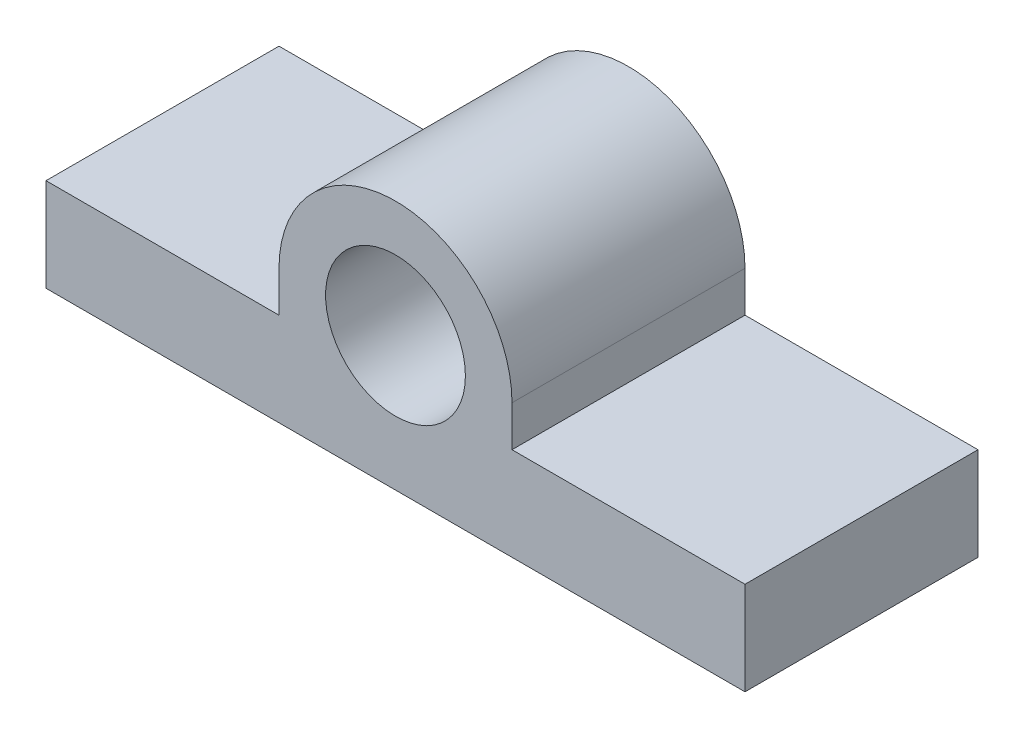
SolidWorks part; units mm, degrees
ref_plane "Front Plane" through (0, 0, 0) normal (0, 0, 1) x (1, 0, 0)
ref_plane "Top Plane" through (0, 0, 0) normal (0, 1, 0) x (1, 0, 0)
ref_plane "Right Plane" through (0, 0, 0) normal (1, 0, 0) x (0, 0, -1)
sketch "Sketch1" plane through (0, 0, 0) normal (0, 0, 1) x (1, 0, 0)
  line L2 (-21.1029, -0.5294) -> (-21.1029, -5.6094)
  line L4 (16.9971, -0.5294) -> (16.9971, -5.6094)
  line L9 (-21.1029, -0.5294) -> (-8.4029, -0.5294)
  line L11 (16.9971, -0.5294) -> (4.2971, -0.5294)
  line L14 (-21.1029, -5.6094) -> (16.9971, -5.6094)
  line L15 (-8.4029, 1.6861) -> (-8.4029, -0.5294)
  line L16 (4.2971, 1.6861) -> (4.2971, -0.5294)
  circle A0 centre (-2.0529, 1.6861) radius 3.81
  arc A1 (4.2971, 1.6861) -> (-8.4029, 1.6861) centre (-2.0529, 1.6861) ccw
  point P3 (0, 0)
  point P4 (0, 0)
  point P6 (0, 0)
  dimension "D3" = 7.62
  dimension "D4" = 5.08
  dimension "D5" = 5.08
  dimension "D1" = 2.54
  dimension "D2" = 19.05
  dimension "D6" = 38.1
extrude "Boss-Extrude1" add sketch "Sketch1" along normal blind 12.7
